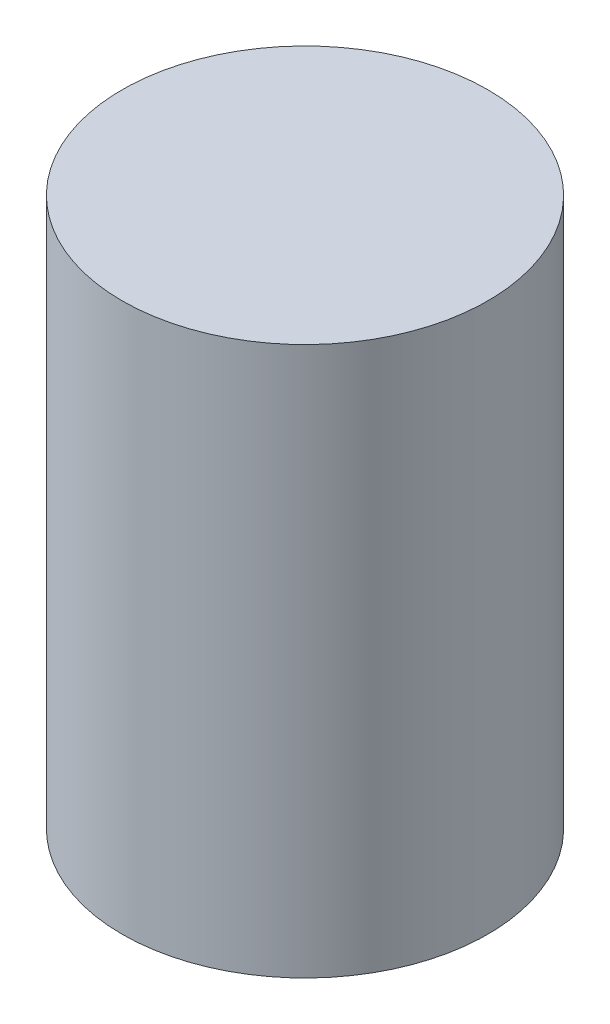
SolidWorks part; units mm, degrees
ref_plane "Front Plane" through (0, 0, 0) normal (0, 0, 1) x (1, 0, 0)
ref_plane "Top Plane" through (0, 0, 0) normal (0, 1, 0) x (1, 0, 0)
ref_plane "Right Plane" through (0, 0, 0) normal (1, 0, 0) x (0, 0, -1)
sketch "Sketch1" plane through (0, 0, 0) normal (0, 1, 0) x (1, 0, 0)
  circle A0 centre (0, 0) radius 500
  dimension "D1" = 1000
extrude "Boss-Extrude1" add sketch "Sketch1" along normal blind 1500
